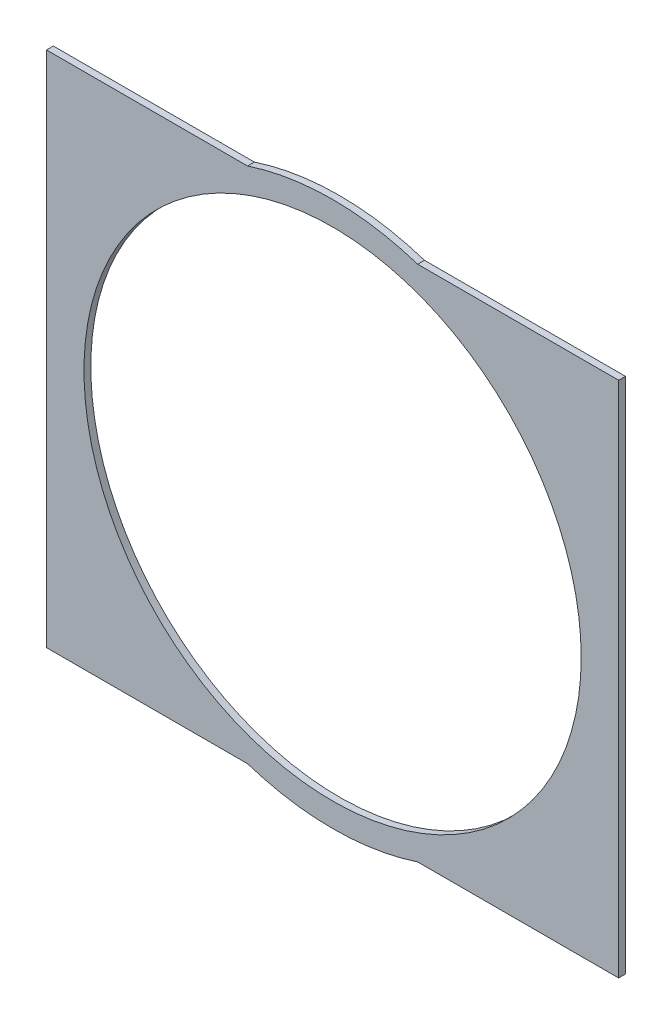
SolidWorks part; units mm, degrees
ref_plane "Płaszczyzna przednia" through (0, 0, 0) normal (0, 0, 1) x (1, 0, 0)
ref_plane "Płaszczyzna górna" through (0, 0, 0) normal (0, 1, 0) x (1, 0, 0)
ref_plane "Płaszczyzna prawa" through (0, 0, 0) normal (1, 0, 0) x (0, 0, -1)
sketch "Sketch1" plane through (0, 0, 0) normal (0, 0, 1) x (1, 0, 0)
  line L1 (0, 0) -> (-84, 0)
  line L2 (0, 0) -> (0, 76)
  line L3 (0, 76) -> (-84, 76)
  line L4 (-84, 0) -> (-84, 76)
  line L5 (0, 0) -> (-84, 76) construction
  line L6 (0, 76) -> (-84, 0) construction
  circle A0 centre (-42, 38) radius 40
  circle A1 centre (-42, 38) radius 36.5
  point P4 (-42, 38)
  dimension "D3" = 80
  dimension "D4" = 73
  dimension "D1" = 84
  dimension "D2" = 76
extrude "Boss-Extrude1" add sketch "Sketch1" along normal blind 1 contours L3 A0 L1 A1 | A0 L3 L4 L1 | A0 L1 L2 L3
